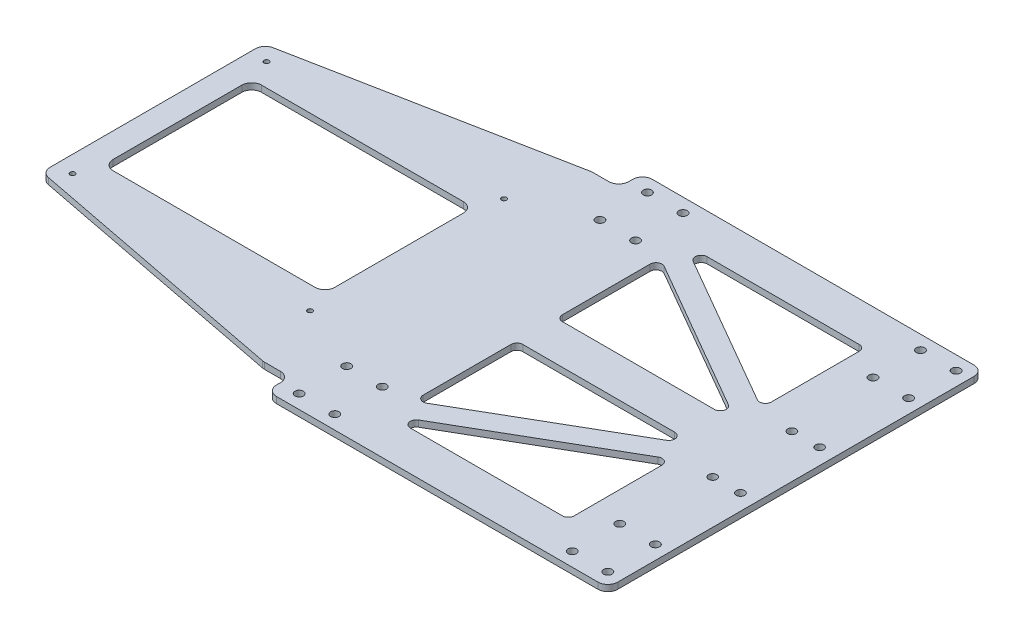
SolidWorks part; units mm, degrees
material "6061 Alloy"
ref_plane "Front Plane" through (0, 0, 0) normal (0, 0, 1) x (1, 0, 0)
ref_plane "Top Plane" through (0, 0, 0) normal (0, 1, 0) x (1, 0, 0)
ref_plane "Right Plane" through (0, 0, 0) normal (1, 0, 0) x (0, 0, -1)
sketch "Sketch1" plane through (0, 0, 0) normal (0, 1, 0) x (1, 0, 0)
  line L1 (-162.5, -95) -> (162.5, -95)
  line L2 (-162.5, -95) -> (-162.5, 95)
  line L3 (-162.5, 95) -> (162.5, 95)
  line L4 (162.5, -95) -> (162.5, 95)
  line L5 (-162.5, -95) -> (162.5, 95) construction
  line L6 (-162.5, 95) -> (162.5, -95) construction
  point P0 (0, 0)
  dimension "D1" = 190
  dimension "D2" = 325
extrude "Platform" add sketch "Sketch1" along normal blind 3.175
sketch "Sketch2" plane through (0, 3.175, 0) normal (0, 1, 0) x (1, 0, 0)
  line L0 (0, 0) -> (-94, 0) construction
  line L1 (-150, -37.5) -> (-38, -37.5)
  line L2 (-150, -37.5) -> (-150, 37.5)
  line L3 (-150, 37.5) -> (-38, 37.5)
  line L4 (-38, -37.5) -> (-38, 37.5)
  line L5 (-150, -37.5) -> (-38, 37.5) construction
  line L6 (-150, 37.5) -> (-38, -37.5) construction
  line L7 (-162.5, 95) -> (-162.5, -95) construction
  point P0 (-94, 0)
  dimension "D1" = 112
  dimension "D2" = 75
  dimension "D3" = 12.5
extrude "Microplate Cutout" cut sketch "Sketch2" against normal through all
sketch "Sketch3" plane through (0, 3.175, 0) normal (0, 1, 0) x (1, 0, 0)
  line L0 (147.5, 0) -> (0, 0) construction
  line L1 (140.5, -20) -> (154.5, -20) construction
  line L2 (140.5, -20) -> (140.5, 20) construction
  line L3 (140.5, 20) -> (154.5, 20) construction
  line L4 (154.5, -20) -> (154.5, 20) construction
  line L5 (140.5, -20) -> (154.5, 20) construction
  line L6 (140.5, 20) -> (154.5, -20) construction
  line L7 (162.5, -95) -> (162.5, 95) construction
  circle A0 centre (140.5, 20) radius 1
  circle A1 centre (154.5, 20) radius 1
  circle A2 centre (154.5, -20) radius 1
  circle A3 centre (140.5, -20) radius 1
  point P0 (147.5, 0)
  dimension "D1" = 2
  dimension "D2" = 8
  dimension "D3" = 14
  dimension "D4" = 40
extrude "Lead Nut Hole Positions" cut sketch "Sketch3" against normal through all
sketch "Sketch4" plane through (0, 3.175, 0) normal (0, 1, 0) x (1, 0, 0)
  line L0 (8.5, 0) -> (8.5, 76) construction
  line L1 (-0.5, 64) -> (17.5, 64) construction
  line L2 (-0.5, 64) -> (-0.5, 88) construction
  line L3 (-0.5, 88) -> (17.5, 88) construction
  line L4 (17.5, 64) -> (17.5, 88) construction
  line L5 (-0.5, 64) -> (17.5, 88) construction
  line L6 (-0.5, 88) -> (17.5, 64) construction
  line L7 (8.5, 0) -> (162.5, 0) construction
  line L8 (162.5, -95) -> (162.5, 95) construction
  line L9 (-0.5, -88) -> (17.5, -64) construction
  line L10 (-0.5, -64) -> (17.5, -88) construction
  line L11 (17.5, -64) -> (17.5, -88) construction
  line L12 (-0.5, -88) -> (17.5, -88) construction
  line L13 (-0.5, -64) -> (-0.5, -88) construction
  line L14 (-0.5, -64) -> (17.5, -64) construction
  circle A0 centre (17.5, 88) radius 2.125
  circle A1 centre (17.5, 64) radius 2.125
  circle A2 centre (-0.5, 88) radius 2.125
  circle A3 centre (-0.5, 64) radius 2.125
  circle A4 centre (-0.5, -64) radius 2.125
  circle A5 centre (-0.5, -88) radius 2.125
  circle A6 centre (17.5, -64) radius 2.125
  circle A7 centre (17.5, -88) radius 2.125
  point P0 (8.5, 76)
  point P23 (8.5, -76)
  dimension "D3" = 4.25
  dimension "D1" = 18
  dimension "D2" = 24
  dimension "D4" = 76
  dimension "D5" = 154
extrude "Linear Bearing Mounting Holes" cut sketch "Sketch4" against normal through all
pattern_linear "LPattern1" count 2 spacing 138 along (1, 0, 0) of "Linear Bearing Mounting Holes"
sketch "Sketch10" plane through (0, 3.175, 0) normal (0, 1, 0) x (1, 0, 0)
  line L0 (-10, -83) -> (-10, 83) construction
  line L1 (-162.5, 95) -> (-10, 95)
  line L2 (-162.5, 95) -> (-162.5, 83)
  line L3 (-162.5, 83) -> (-10, 83)
  line L4 (-10, 95) -> (-10, 83)
  line L5 (-162.5, -95) -> (-10, -95)
  line L6 (-162.5, -95) -> (-162.5, -83)
  line L7 (-162.5, -83) -> (-10, -83)
  line L8 (-10, -95) -> (-10, -83)
  dimension "D1" = 12
  dimension "D2" = 10
extrude "Cut-Extrude1" cut sketch "Sketch10" against normal through all
chamfer "Chamfer1" distance 27 angle 79 2 edges at (-162.5, 1.5875, -83) (-162.5, 1.5875, 83)
fillet "Fillet1" radius 5 14 edges at (162.5, 1.5875, 95) (162.5, 1.5875, -95) (-38, 1.5875, 37.5) (-150, 1.5875, 37.5) (-38, 1.5875, -37.5) (-150, 1.5875, -37.5) (-23.597, 1.5875, 83) (-10, 1.5875, 83) (-10, 1.5875, 95) (-10, 1.5875, -95) (-10, 1.5875, -83) (-23.597, 1.5875, -83) (-162.5, 1.5875, -56) (-162.5, 1.5875, 56)
hole_wizard "M3x0.5 Tapped Hole1" positions "Sketch6" profile "Sketch7" tap size "M3x0.5" standard "ANSI Metric" end condition through all
sketch "Sketch6" plane through (0, 3.175, 0) normal (0, 1, 0) x (1, 0, 0)
  line L1 (-154, -49) -> (-34, -49) construction
  line L2 (-154, -49) -> (-154, 49) construction
  line L3 (-154, 49) -> (-34, 49) construction
  line L4 (-34, -49) -> (-34, 49) construction
  line L5 (-154, -49) -> (-34, 49) construction
  line L6 (-154, 49) -> (-34, -49) construction
  line L7 (-94, 0) -> (0, 0) construction
  line L9 (-94, 37.5) -> (-94, 0) construction
  line L10 (-43, 37.5) -> (-145, 37.5) construction
  point P1 (-94, 0)
  point P2 (-34, 49)
  point P89 (-154, -49)
  point P90 (-154, 49)
  point P91 (-34, -49)
  dimension "D1" = 120
  dimension "D2" = 98
sketch "Sketch7" plane through (-94, 3.175, 0) normal (1, 0, 0) x (0, 0, 1)
  line L0 (0, 0) -> (0, 3.175)
  line L1 (0, 3.175) -> (1.25, 3.175)
  line L2 (1.25, 3.175) -> (1.25, 0)
  line L5 (1.25, 0) -> (0, 0)
  line L11 (0, -6.35) -> (0, 107.95) construction
  dimension "Thru Tap Drill Dia." = 2.5
  dimension "Thru Tap Drill Depth" = 3.175
cosmetic thread "Hole Thread1" parameters "D2"=3
cosmetic thread "Hole Thread4" parameters "D2"=3
cosmetic thread "Hole Thread9" parameters "D2"=3
cosmetic thread "Hole Thread10" parameters "D2"=3
hole_wizard "M5x0.8 Tapped Hole1" positions "Sketch8" profile "Sketch9" tap size "M5x0.8" standard "ANSI Metric" end condition through all
sketch "Sketch8" plane through (0, 3.175, 0) normal (0, 1, 0) x (1, 0, 0)
  point P0 (154.5, 20)
  point P3 (140.5, 20)
  point P6 (154.5, -20)
  point P9 (140.5, -20)
sketch "Sketch9" plane through (154.5, 3.175, -20) normal (1, 0, 0) x (0, 0, 1)
  line L0 (0, 0) -> (0, 3.175)
  line L1 (0, 3.175) -> (2.1, 3.175)
  line L2 (2.1, 3.175) -> (2.1, 0)
  line L5 (2.1, 0) -> (0, 0)
  line L11 (0, -6.35) -> (0, 107.95) construction
  dimension "Thru Tap Drill Dia." = 4.2
  dimension "Thru Tap Drill Depth" = 3.175
cosmetic thread "Hole Thread5" parameters "D2"=5
cosmetic thread "Hole Thread6" parameters "D2"=5
cosmetic thread "Hole Thread7" parameters "D2"=5
cosmetic thread "Hole Thread8" parameters "D2"=5
sketch "Sketch12" plane through (0, 3.175, 0) normal (0, 1, 0) x (1, 0, 0)
  line L0 (0, 0) -> (162.5, 0) construction
  line L2 (122.5, 22.4611) -> (31.5, 75)
  line L3 (31.5, 75) -> (122.5, 75)
  line L4 (122.5, 75) -> (122.5, 22.4611)
  line L5 (122.5, 10) -> (31.5, 62.5389)
  line L6 (31.5, 62.5389) -> (31.5, 10)
  line L7 (31.5, 10) -> (122.5, 10)
  line L8 (157.5, 95) -> (-5, 95) construction
  line L9 (162.5, -90) -> (162.5, 90) construction
  line L10 (31.5, 62.5389) -> (31.5, 75) construction
  line L11 (31.5, 10) -> (11.5, 10) construction
  line L18 (-18, 39.493) -> (11.5, 39.493) construction
  line L21 (-18, 39.493) -> (-18, 22.4611) construction
  line L22 (-18, 10) -> (11.5, 10) construction
  line L24 (-38, -32.5) -> (-38, 32.5) construction
  line L25 (122.5, 22.4611) -> (117.1042, 13.1153) construction
  line L26 (122.5, -22.4611) -> (117.1042, -13.1153) construction
  line L27 (11.5, 27.0318) -> (6.1042, 36.3777) construction
  line L28 (31.5, -62.5389) -> (31.5, -75) construction
  line L35 (31.5, -10) -> (122.5, -10)
  line L36 (31.5, -62.5389) -> (31.5, -10)
  line L37 (122.5, -10) -> (31.5, -62.5389)
  line L38 (31.5, -75) -> (122.5, -75)
  line L39 (122.5, -22.4611) -> (31.5, -75)
  line L40 (122.5, -75) -> (122.5, -22.4611)
  line L41 (11.5, 27.0318) -> (11.5, 39.493) construction
  line L42 (11.5, -27.0318) -> (11.5, -39.493) construction
  line L44 (-18, 22.4611) -> (11.5, 39.493) construction
  line L45 (11.5, 10) -> (11.5, 27.0318) construction
  line L46 (11.5, 27.0318) -> (-18, 10) construction
  line L47 (11.5, -27.0318) -> (6.1042, -36.3777) construction
  line L48 (11.5, -27.0318) -> (-18, -10) construction
  line L49 (11.5, -10) -> (11.5, -27.0318) construction
  line L50 (-18, -22.4611) -> (11.5, -39.493) construction
  line L52 (-18, -10) -> (11.5, -10) construction
  line L53 (-18, -39.493) -> (-18, -22.4611) construction
  line L54 (-18, -39.493) -> (11.5, -39.493) construction
  dimension "D1" = 30
  dimension "D2" = 30
  dimension "D3" = 20
  dimension "D4" = 40
  dimension "D5" = 91
  dimension "D6" = 10
  dimension "D7" = 30
  dimension "D8" = 20
  dimension "D9" = 20
  dimension "D10" = 10.7917
extrude "Cut-Extrude3" cut sketch "Sketch12" against normal through all
fillet "Fillet3" radius 3 12 edges at (122.5, 1.5875, -22.4611) (122.5, 1.5875, -75) (31.5, 1.5875, -10) (31.5, 1.5875, -62.5389) (122.5, 1.5875, -10) (31.5, 1.5875, -75) (31.5, 1.5875, 10) (122.5, 1.5875, 10) (31.5, 1.5875, 62.5389) (122.5, 1.5875, 75) (122.5, 1.5875, 22.4611) (31.5, 1.5875, 75)
sketch "Sketch13" [suppressed] plane through (0, 0, 0) normal (0, 1, 0) x (1, 0, 0)
  line L0 (-1.7463, 0) -> (1.7463, 0) construction
  line L1 (-162.5, 0) -> (-150, 0)
  line L2 (-162.5, 51.8783) -> (-162.5, -51.8783) construction
  line L3 (-150, 32.5) -> (-150, -32.5) construction
  circle A0 centre (-156.25, 0) radius 4
  dimension "D1" = 8
sketch "Sketch14" [suppressed] plane through (0, 3.175, 0) normal (0, 1, 0) x (1, 0, 0)
  circle A0 centre (-156.25, 0) radius 4 construction
  circle A1 centre (-156.25, 0) radius 4
split line "Split Line1" [suppressed]
